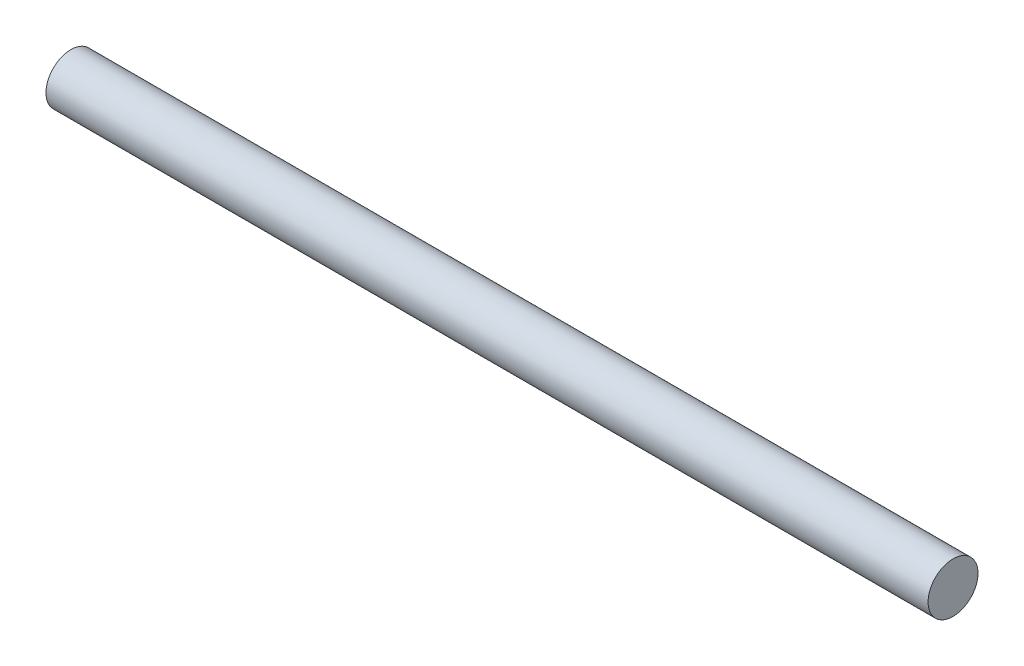
SolidWorks part; units mm, degrees
material "1.0038 (S235JRG2)"
ref_plane "Ön Düzlem" through (0, 0, 0) normal (0, 0, 1) x (1, 0, 0)
ref_plane "Üst Düzlem" through (0, 0, 0) normal (0, 1, 0) x (1, 0, 0)
ref_plane "Sağ Düzlem" through (0, 0, 0) normal (1, 0, 0) x (0, 0, -1)
sketch "Çizim1" plane through (0, 0, 0) normal (1, 0, 0) x (0, 0, -1)
  circle A0 centre (0, 0) radius 6
  dimension "D1" = 12
extrude "Yükseklik-Ekstrüzyon1" add sketch "Çizim1" along normal blind 212
